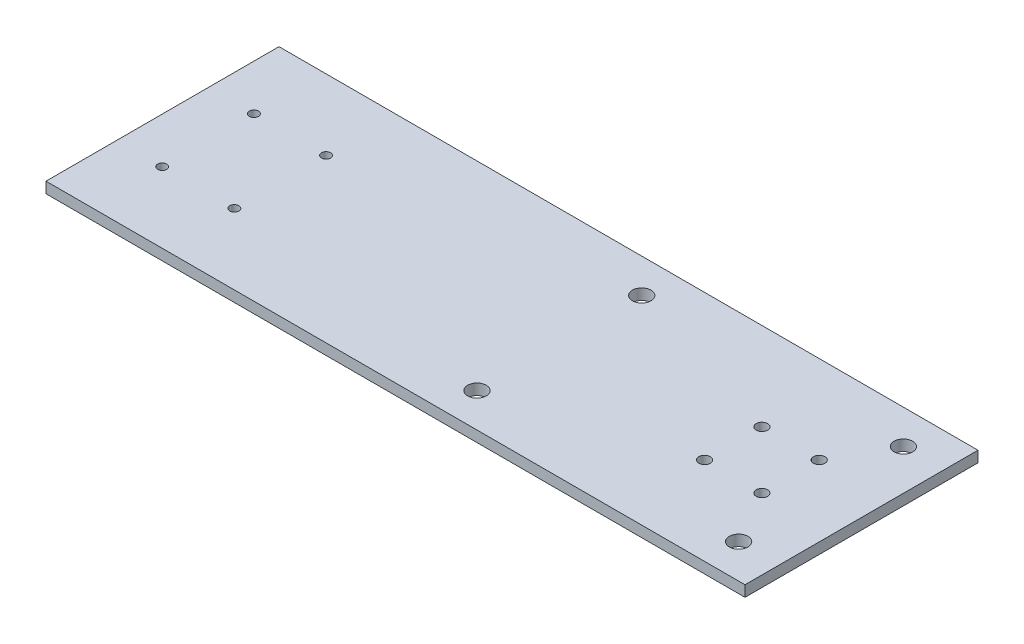
SolidWorks part; units mm, degrees
material "6061 Alloy"
ref_plane "Front Plane" through (0, 0, 0) normal (0, 0, 1) x (1, 0, 0)
ref_plane "Top Plane" through (0, 0, 0) normal (0, 1, 0) x (1, 0, 0)
ref_plane "Right Plane" through (0, 0, 0) normal (1, 0, 0) x (0, 0, -1)
sketch "Sketch2" plane through (0, 0, 0) normal (0, 1, 0) x (1, 0, 0)
  line L0 (0, 25.4) -> (0, 127)
  line L1 (0, 127) -> (304.8, 127)
  line L2 (304.8, 127) -> (304.8, 25.4)
  line L3 (304.8, 25.4) -> (0, 25.4)
  line L4 (0, 76.2) -> (304.8, 76.2) construction
  line L5 (135.2352, 128.2257) -> (135.2352, 26.6257) construction
  line L6 (248.8644, 63.7) -> (273.8644, 88.7) construction
  line L7 (248.8644, 88.7) -> (273.8644, 63.7) construction
  line L8 (168.6768, 40.2828) -> (173.0424, 40.2828) construction
  line L9 (173.0424, 40.2828) -> (173.0424, 112.1172) construction
  line L10 (287.143, 40.2828) -> (287.143, 112.1172) construction
  line L11 (19.8761, 96.2) -> (19.8761, 56.2) construction
  line L12 (51.3288, 96.2) -> (51.3288, 56.2) construction
  circle A0 centre (248.8644, 88.7) radius 2.5
  circle A1 centre (248.8644, 63.7) radius 2.5
  circle A2 centre (273.8644, 63.7) radius 2.5
  circle A3 centre (273.8644, 88.7) radius 2.5
  circle A4 centre (173.0424, 40.2828) radius 4.05
  circle A5 centre (173.0424, 112.1172) radius 4.05
  circle A6 centre (287.143, 40.2828) radius 4.05
  circle A7 centre (287.143, 112.1172) radius 4.05
  circle A8 centre (19.8761, 56.2) radius 2
  circle A9 centre (51.3288, 56.2) radius 2
  circle A10 centre (51.3288, 96.2) radius 2
  circle A11 centre (19.8761, 96.2) radius 2
extrude "Boss-Extrude1" add sketch "Sketch2" along normal blind 4.7625
